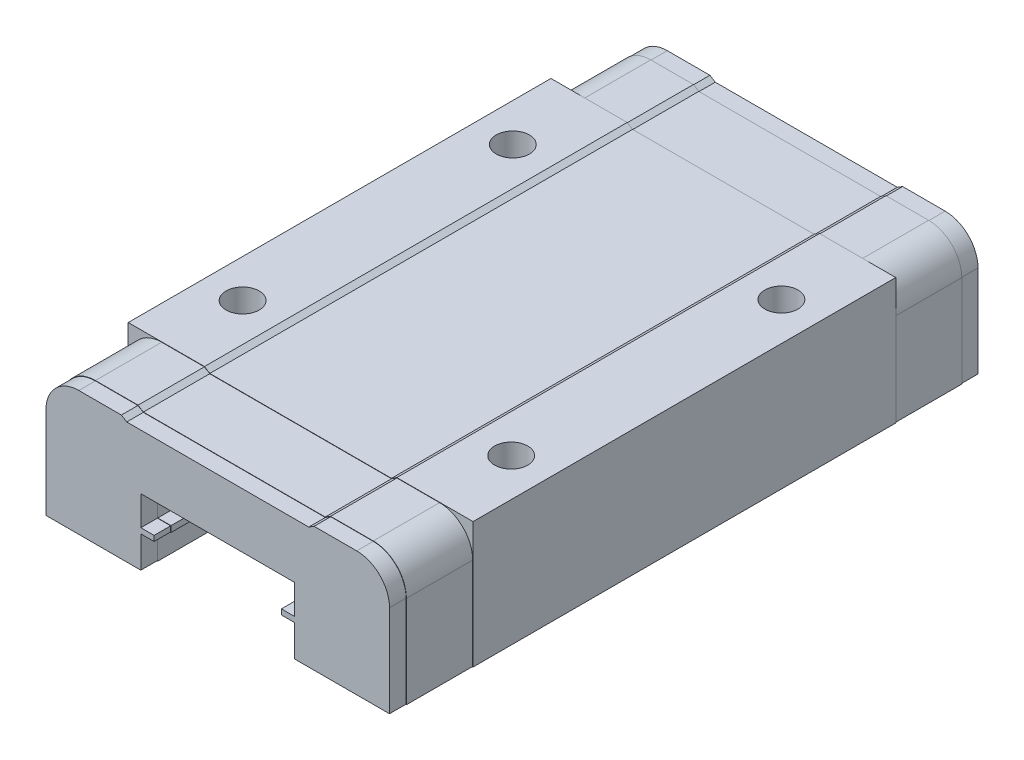
SolidWorks part; units mm, degrees
ref_plane "Front Plane" through (0, 0, 0) normal (0, 0, 1) x (1, 0, 0)
ref_plane "Top Plane" through (0, 0, 0) normal (0, 1, 0) x (1, 0, 0)
ref_plane "Right Plane" through (0, 0, 0) normal (1, 0, 0) x (0, 0, -1)
sketch "Sketch1" plane through (0, 0, 0) normal (0, 0, 1) x (1, 0, 0)
  line L1 (13.208, 0.254) -> (13.208, -9.398)
  line L2 (13.208, -9.398) -> (5.842, -9.398)
  line L3 (5.842, -9.398) -> (5.842, -6.985)
  line L4 (5.842, -6.985) -> (4.826, -6.985)
  line L8 (5.842, -4.318) -> (-5.842, -4.318)
  line L9 (-5.842, -4.318) -> (-5.842, -6.477)
  line L10 (-5.842, -6.477) -> (-4.826, -6.477)
  line L11 (-4.826, -6.477) -> (-4.826, -6.985)
  line L12 (-4.826, -6.985) -> (-5.842, -6.985)
  line L13 (-5.842, -6.985) -> (-5.842, -9.398)
  line L14 (-5.842, -9.398) -> (-13.208, -9.398)
  line L15 (-13.208, -9.398) -> (-13.208, 0.254)
  line L17 (-13.208, 0.254) -> (-7.3675, 0.254)
  line L18 (4.826, -6.985) -> (4.826, -6.477)
  line L19 (4.826, -6.477) -> (5.842, -6.477)
  line L20 (5.842, -6.477) -> (5.842, -4.318)
  line L21 (0, 6.3337) -> (0, -7.3685) construction
  line L22 (-7.3675, 0.254) -> (-6.9583, 0)
  line L23 (-6.9583, 0) -> (6.9583, 0)
  line L24 (6.9583, 0) -> (7.3675, 0.254)
  line L25 (7.3675, 0.254) -> (13.208, 0.254)
  dimension "D1" = 26.416
  dimension "D2" = 7.366
  dimension "D3" = 9.652
  dimension "D4" = 0.254
  dimension "D5" = 4.318
  dimension "D6" = 0.508
  dimension "D7" = 1.016
  dimension "D8" = 2.159
extrude "Boss-Extrude1" add sketch "Sketch1" along normal mid plane 32.385
sketch "Sketch2" plane through (0, 0.254, 0) normal (0, 1, 0) x (1, 0, 0)
  line L0 (-10.2877, 10.3505) -> (10.2877, 10.3505) construction
  line L1 (-10.2877, 16.1925) -> (-10.2877, -16.1925) construction
  line L2 (-7.3675, 16.1925) -> (-13.208, 16.1925) construction
  line L3 (-7.3675, -16.1925) -> (-13.208, -16.1925) construction
  line L4 (10.2877, 16.1925) -> (10.2877, -16.1925) construction
  line L5 (13.208, 16.1925) -> (7.3675, 16.1925) construction
  line L6 (13.208, -16.1925) -> (7.3675, -16.1925) construction
  circle A0 centre (-10.2877, 10.3505) radius 1.27
  circle A1 centre (10.2877, 10.3505) radius 1.27
  circle A2 centre (10.2877, -10.3505) radius 1.27
  circle A3 centre (-10.2877, -10.3505) radius 1.27
  point P10 (-10.2877, 11.6205)
  point P21 (-10.2877, -11.6205)
  dimension "D5" = 2.54
  dimension "D3" = 4.572
  dimension "D4" = 4.572
  dimension "D1" = 2
  dimension "D2" = 2
extrude "Cut-Extrude1" cut sketch "Sketch2" against normal blind 5.08
sketch "Sketch3" plane through (0, 0, 16.1925) normal (0, 0, 1) x (1, 0, 0)
  line L76 (5.8674, -4.2926) -> (5.8674, -6.5024)
  line L77 (5.8674, -6.5024) -> (4.8514, -6.5024)
  line L78 (4.8514, -6.5024) -> (4.8514, -6.9596)
  line L79 (4.8514, -6.9596) -> (5.8674, -6.9596)
  line L80 (5.8674, -6.9596) -> (5.8674, -9.3726)
  line L81 (5.8674, -9.3726) -> (13.1826, -9.3726)
  line L82 (13.1826, -9.3726) -> (13.1826, 0.2286)
  line L83 (13.1826, 0.2286) -> (7.3747, 0.2286)
  line L84 (7.3747, 0.2286) -> (6.9655, -0.0254)
  line L85 (6.9655, -0.0254) -> (-6.9655, -0.0254)
  line L86 (-6.9655, -0.0254) -> (-7.3747, 0.2286)
  line L87 (-7.3747, 0.2286) -> (-13.1826, 0.2286)
  line L88 (-13.1826, 0.2286) -> (-13.1826, -9.3726)
  line L89 (-13.1826, -9.3726) -> (-5.8674, -9.3726)
  line L90 (-5.8674, -9.3726) -> (-5.8674, -6.9596)
  line L91 (-5.8674, -6.9596) -> (-4.8514, -6.9596)
  line L92 (-4.8514, -6.9596) -> (-4.8514, -6.5024)
  line L93 (-4.8514, -6.5024) -> (-5.8674, -6.5024)
  line L94 (-5.8674, -6.5024) -> (-5.8674, -4.2926)
  line L95 (-5.8674, -4.2926) -> (5.8674, -4.2926)
  line L96 (5.8674, -4.2926) -> (5.8674, -6.5024)
  line L97 (5.8674, -6.5024) -> (4.8514, -6.5024)
  line L98 (4.8514, -6.5024) -> (4.8514, -6.9596)
  line L99 (4.8514, -6.9596) -> (5.8674, -6.9596)
  line L100 (5.8674, -6.9596) -> (5.8674, -9.3726)
  line L101 (5.8674, -9.3726) -> (13.1826, -9.3726)
  line L102 (13.1826, -9.3726) -> (13.1826, -2.3114)
  line L103 (10.6426, 0.2286) -> (7.3747, 0.2286)
  line L104 (7.3747, 0.2286) -> (6.9655, -0.0254)
  line L105 (6.9655, -0.0254) -> (-6.9655, -0.0254)
  line L106 (-6.9655, -0.0254) -> (-7.3747, 0.2286)
  line L107 (-7.3747, 0.2286) -> (-10.6426, 0.2286)
  line L108 (-13.1826, -2.3114) -> (-13.1826, -9.3726)
  line L109 (-13.1826, -9.3726) -> (-5.8674, -9.3726)
  line L110 (-5.8674, -9.3726) -> (-5.8674, -6.9596)
  line L111 (-5.8674, -6.9596) -> (-4.8514, -6.9596)
  line L112 (-4.8514, -6.9596) -> (-4.8514, -6.5024)
  line L113 (-4.8514, -6.5024) -> (-5.8674, -6.5024)
  line L114 (-5.8674, -6.5024) -> (-5.8674, -4.2926)
  line L115 (-5.8674, -4.2926) -> (5.8674, -4.2926)
  arc A2 (13.1826, -2.3114) -> (10.6426, 0.2286) centre (10.6426, -2.3114) ccw
  arc A3 (-13.1826, -2.3114) -> (-10.6426, 0.2286) centre (-10.6426, -2.3114) cw
  dimension "D2" = 2.54
  dimension "D1" = 0.0254
extrude "Boss-Extrude2" add sketch "Sketch3" along direction (0, 0, 1) on the side of the normal blind 5.08
sketch "Sketch5" plane through (0, 0, 21.2725) normal (0, 0, 1) x (1, 0, 0)
  line L116 (13.1572, -9.3472) -> (13.1572, -2.3114)
  line L117 (10.6426, 0.2032) -> (7.382, 0.2032)
  line L118 (7.382, 0.2032) -> (6.9728, -0.0508)
  line L119 (6.9728, -0.0508) -> (-6.9728, -0.0508)
  line L120 (-6.9728, -0.0508) -> (-7.382, 0.2032)
  line L121 (-7.382, 0.2032) -> (-10.6426, 0.2032)
  line L122 (-13.1572, -2.3114) -> (-13.1572, -9.3472)
  line L123 (-13.1572, -9.3472) -> (-5.8928, -9.3472)
  line L124 (-5.8928, -9.3472) -> (-5.8928, -6.9342)
  line L125 (-5.8928, -6.9342) -> (-4.8768, -6.9342)
  line L126 (-4.8768, -6.9342) -> (-4.8768, -6.5278)
  line L127 (-4.8768, -6.5278) -> (-5.8928, -6.5278)
  line L128 (-5.8928, -6.5278) -> (-5.8928, -4.2672)
  line L129 (-5.8928, -4.2672) -> (5.8928, -4.2672)
  line L130 (5.8928, -4.2672) -> (5.8928, -6.5278)
  line L131 (5.8928, -6.5278) -> (4.8768, -6.5278)
  line L132 (4.8768, -6.5278) -> (4.8768, -6.9342)
  line L133 (4.8768, -6.9342) -> (5.8928, -6.9342)
  line L134 (5.8928, -6.9342) -> (5.8928, -9.3472)
  line L135 (5.8928, -9.3472) -> (13.1572, -9.3472)
  line L136 (13.1572, -9.3472) -> (13.1572, -2.3114)
  line L137 (10.6426, 0.2032) -> (7.382, 0.2032)
  line L138 (7.382, 0.2032) -> (6.9728, -0.0508)
  line L139 (6.9728, -0.0508) -> (-6.9728, -0.0508)
  line L140 (-6.9728, -0.0508) -> (-7.382, 0.2032)
  line L141 (-7.382, 0.2032) -> (-10.6426, 0.2032)
  line L142 (-13.1572, -2.3114) -> (-13.1572, -9.3472)
  line L143 (-13.1572, -9.3472) -> (-5.8928, -9.3472)
  line L144 (-5.8928, -9.3472) -> (-5.8928, -6.9342)
  line L145 (-5.8928, -6.9342) -> (-4.8768, -6.9342)
  line L146 (-4.8768, -6.9342) -> (-4.8768, -6.5278)
  line L147 (-4.8768, -6.5278) -> (-5.8928, -6.5278)
  line L148 (-5.8928, -6.5278) -> (-5.8928, -4.2672)
  line L149 (-5.8928, -4.2672) -> (5.8928, -4.2672)
  line L150 (5.8928, -4.2672) -> (5.8928, -6.5278)
  line L151 (5.8928, -6.5278) -> (4.8768, -6.5278)
  line L152 (4.8768, -6.5278) -> (4.8768, -6.9342)
  line L153 (4.8768, -6.9342) -> (5.8928, -6.9342)
  line L154 (5.8928, -6.9342) -> (5.8928, -9.3472)
  line L155 (5.8928, -9.3472) -> (13.1572, -9.3472)
  arc A12 (13.1572, -2.3114) -> (10.6426, 0.2032) centre (10.6426, -2.3114) ccw
  arc A13 (-10.6426, 0.2032) -> (-13.1572, -2.3114) centre (-10.6426, -2.3114) ccw
  arc A14 (13.1572, -2.3114) -> (10.6426, 0.2032) centre (10.6426, -2.3114) ccw
  arc A15 (-10.6426, 0.2032) -> (-13.1572, -2.3114) centre (-10.6426, -2.3114) ccw
  dimension "D1" = 0.0254
extrude "Boss-Extrude3" add sketch "Sketch5" along normal blind 1.27 contours L141 A15 L142 L143 L144 L145 L146 L147 L148 L149 L150 L151 L152 L153 L154 L155 L136 A14 L137 L138 L139 L140
mirror "Mirror2" about plane through (0, 0, 0) normal (0, 0, 1) of "Boss-Extrude3", "Boss-Extrude2"
